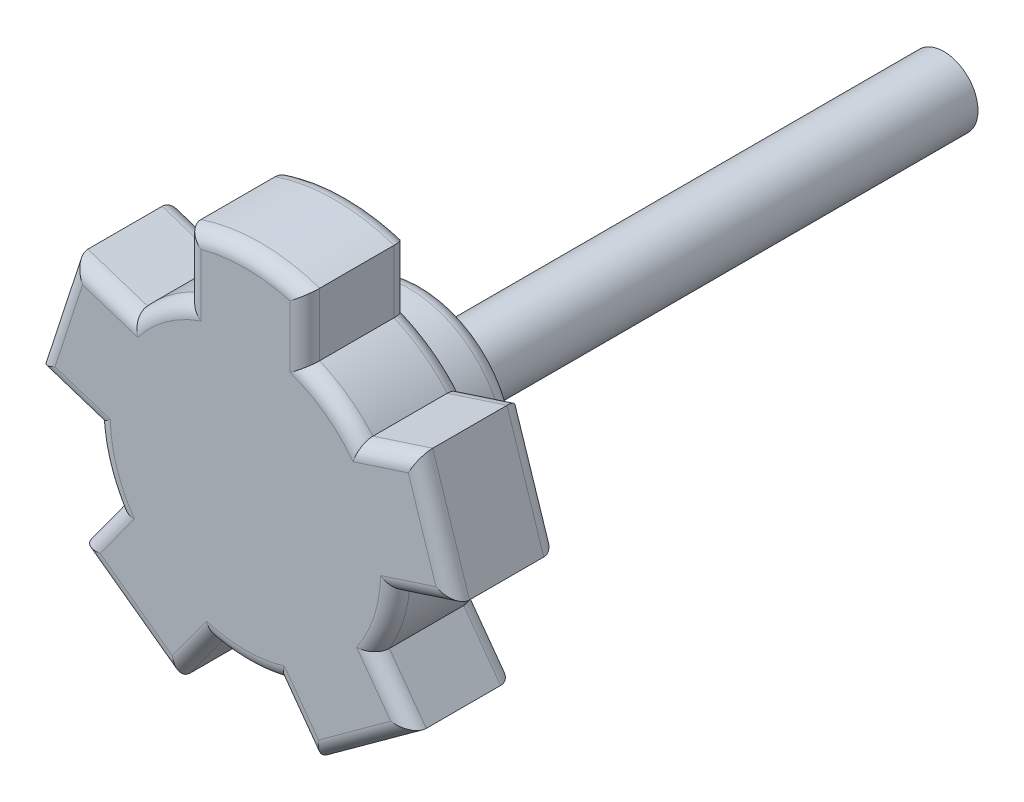
SolidWorks part; units mm, degrees
ref_plane "Front Plane" through (0, 0, 0) normal (0, 0, 1) x (1, 0, 0)
ref_plane "Top Plane" through (0, 0, 0) normal (0, 1, 0) x (1, 0, 0)
ref_plane "Right Plane" through (0, 0, 0) normal (1, 0, 0) x (0, 0, -1)
sketch "Sketch1" plane through (0, 0, 0) normal (0, 0, 1) x (1, 0, 0)
  circle A0 centre (0, 0) radius 2.921
extrude "Extrude1" add sketch "Sketch1" along normal blind 44.45
sketch "Sketch2" plane through (0, 0, 44.45) normal (0, 0, 1) x (1, 0, 0)
  circle A0 centre (0, 0) radius 8.255
extrude "Extrude2" add sketch "Sketch2" along normal blind 6.35
sketch "Sketch3" plane through (0, 0, 50.8) normal (0, 0, 1) x (1, 0, 0)
  circle A0 centre (0, 0) radius 12.827
extrude "Extrude3" add sketch "Sketch3" along normal blind 8.89
sketch "Sketch4" plane through (0, 0, 59.69) normal (0, 0, 1) x (1, 0, 0)
  line L0 (5.08, 11.7782) -> (5.08, 17.145) construction
  line L1 (-5.08, 11.7782) -> (-5.08, 17.145) construction
  line L2 (9.6319, 8.471) -> (14.7361, 10.1295)
  line L3 (14.7361, 10.1295) -> (17.8757, 0.4667)
  line L4 (0, 12.827) -> (0, 11.557) construction
  line L5 (-5.08, 11.7782) -> (-5.08, 17.145)
  line L6 (12.7715, -1.1917) -> (17.8757, 0.4667)
  line L7 (12.7715, -1.1917) -> (17.8757, 0.4667) construction
  line L8 (-5.08, 17.145) -> (5.08, 17.145)
  line L9 (5.08, 11.7782) -> (5.08, 17.145)
  line L10 (9.6319, 8.471) -> (14.7361, 10.1295) construction
  line L11 (12.1992, 3.9638) -> (10.9914, 3.5713) construction
  line L12 (11.0328, -6.5428) -> (14.1874, -10.8846)
  line L13 (14.1874, -10.8846) -> (5.9678, -16.8565)
  line L14 (2.8132, -12.5147) -> (5.9678, -16.8565)
  line L15 (2.8132, -12.5147) -> (5.9678, -16.8565) construction
  line L16 (11.0328, -6.5428) -> (14.1874, -10.8846) construction
  line L17 (7.5395, -10.3773) -> (6.793, -9.3498) construction
  line L18 (-2.8132, -12.5147) -> (-5.9678, -16.8565)
  line L19 (-5.9678, -16.8565) -> (-14.1874, -10.8846)
  line L20 (-11.0328, -6.5428) -> (-14.1874, -10.8846)
  line L21 (-11.0328, -6.5428) -> (-14.1874, -10.8846) construction
  line L22 (-2.8132, -12.5147) -> (-5.9678, -16.8565) construction
  line L23 (-7.5395, -10.3773) -> (-6.793, -9.3498) construction
  line L24 (-12.7715, -1.1917) -> (-17.8757, 0.4667)
  line L25 (-17.8757, 0.4667) -> (-14.7361, 10.1295)
  line L26 (-9.6319, 8.471) -> (-14.7361, 10.1295)
  line L27 (-9.6319, 8.471) -> (-14.7361, 10.1295) construction
  line L28 (-12.7715, -1.1917) -> (-17.8757, 0.4667) construction
  line L29 (-12.1992, 3.9638) -> (-10.9914, 3.5713) construction
  circle A0 centre (0, 0) radius 12.827 construction
  arc A1 (-5.08, 11.7782) -> (5.08, 11.7782) centre (0, 0) cw
  arc A2 (9.6319, 8.471) -> (12.7715, -1.1917) centre (0, 0) cw
  arc A3 (11.0328, -6.5428) -> (2.8132, -12.5147) centre (0, 0) cw
  arc A4 (-2.8132, -12.5147) -> (-11.0328, -6.5428) centre (0, 0) cw
  arc A5 (-12.7715, -1.1917) -> (-9.6319, 8.471) centre (0, 0) cw
sketch "Sketch6" plane through (0, 0, 0) normal (0, 1, 0) x (1, 0, 0)
  line L0 (0, -62.9081) -> (0, 0) construction
extrude "Extrude6" add sketch "Sketch4" against normal up to surface (8.89 mm away) up to face at (12.827, 0, 50.8)
sketch "Sketch7" plane through (0, 0, 59.69) normal (0, 0, 1) x (1, 0, 0)
  line L0 (5.08, 17.145) -> (-5.08, 17.145)
  arc A0 (-5.08, 17.145) -> (5.08, 17.145) centre (0, 2.2854) cw
extrude "Extrude7" add sketch "Sketch7" against normal up to surface (8.89 mm away) up to face at (0, 0, 50.8)
fillet "Fillet1" radius 1.27 42 edges at (7.5395, 10.3773, 50.8) (5.08, 14.4616, 50.8) (5.08, 14.4616, 59.69) (0, 17.9894, 50.8) (0, 17.9894, 59.69) (-5.08, 14.4616, 50.8) (-5.08, 14.4616, 59.69) (-7.5395, 10.3773, 50.8) (8.255, 0, 50.8) (7.5395, 10.3773, 59.69) (-7.5395, 10.3773, 59.69) (8.255, 0, 44.45) (-12.184, 9.3002, 50.8) (-12.184, 9.3002, 59.69) (-16.3059, 5.2981, 50.8) (-16.3059, 5.2981, 59.69) (-15.3236, -0.3625, 50.8) (-15.3236, -0.3625, 59.69) (-12.1992, -3.9638, 50.8) (-12.6101, -8.7137, 50.8) (-12.6101, -8.7137, 59.69) (-10.0776, -13.8706, 50.8) (-10.0776, -13.8706, 59.69) (-4.3905, -14.6856, 50.8) (-4.3905, -14.6856, 59.69) (0, -12.827, 50.8) (4.3905, -14.6856, 50.8) (4.3905, -14.6856, 59.69) (10.0776, -13.8706, 50.8) (10.0776, -13.8706, 59.69) (12.6101, -8.7137, 50.8) (12.6101, -8.7137, 59.69) (12.1992, -3.9638, 50.8) (15.3236, -0.3625, 50.8) (15.3236, -0.3625, 59.69) (16.3059, 5.2981, 50.8) (16.3059, 5.2981, 59.69) (12.184, 9.3002, 50.8) (12.184, 9.3002, 59.69) (12.1992, -3.9638, 59.69) (0, -12.827, 59.69) (-12.1992, -3.9638, 59.69)
